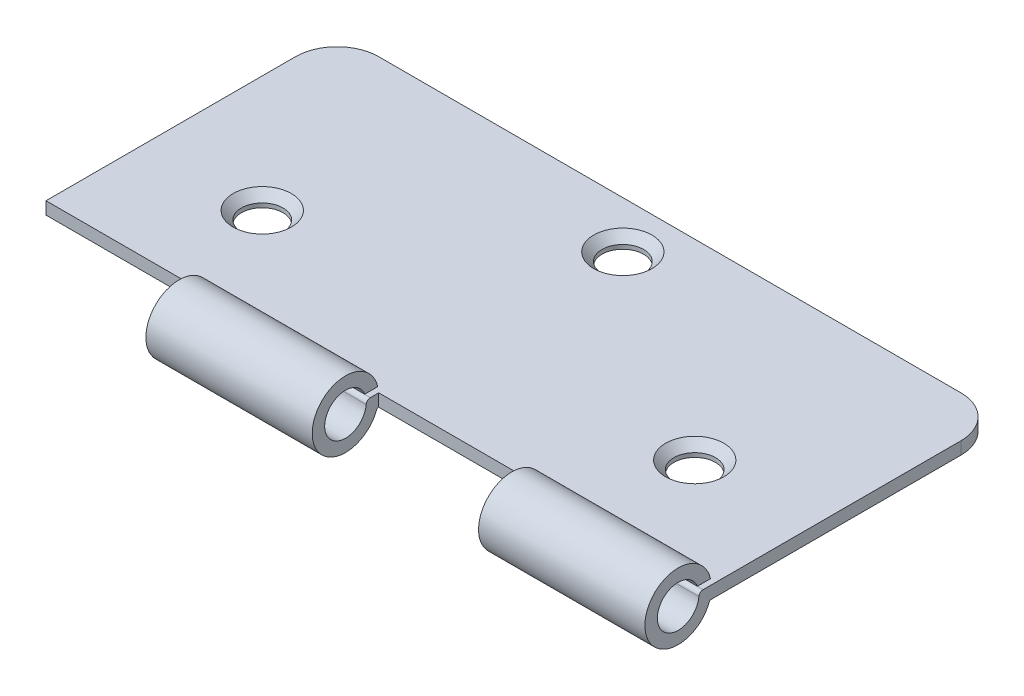
SolidWorks part; units mm, degrees
ref_plane "Front Plane" through (0, 0, 0) normal (0, 0, 1) x (1, 0, 0)
ref_plane "Top Plane" through (0, 0, 0) normal (0, 1, 0) x (1, 0, 0)
ref_plane "Right Plane" through (0, 0, 0) normal (1, 0, 0) x (0, 0, -1)
sketch "Sketch1" plane through (0, 0, 0) normal (0, 1, 0) x (1, 0, 0)
  line L1 (-40, -17.5) -> (40, -17.5)
  line L2 (-40, -17.5) -> (-40, 12.5)
  line L3 (-35, 17.5) -> (35, 17.5)
  line L4 (40, -17.5) -> (40, 12.5)
  line L5 (-40, -17.5) -> (40, 17.5) construction
  line L6 (-40, 17.5) -> (40, -17.5) construction
  arc A0 (35, 17.5) -> (40, 12.5) centre (35, 12.5) cw
  arc A1 (-40, 12.5) -> (-35, 17.5) centre (-35, 12.5) cw
  point P0 (0, 0)
  dimension "D3" = 5
  dimension "D1" = 80
  dimension "D2" = 35
extrude "Boss-Extrude1" add sketch "Sketch1" along normal blind 1.5
sketch "Sketch2" plane through (40, 0, 0) normal (1, 0, 0) x (0, 0, -1)
  line L0 (-17.5, 1.5) -> (-18.5043, 1.5)
  line L1 (-17.5, 0) -> (-17.5553, 0)
  line L2 (-19.1733, 2.1939) -> (-17.6031, 2.1939)
  line L3 (-17.5, 1.5) -> (-17.5, 0)
  arc A0 (-17.6031, 2.1939) -> (-17.7428, -0.1304) centre (-21.4929, 1.2614) ccw
  arc A1 (-19.1733, 2.1939) -> (-19.0024, 1.0436) centre (-21.4929, 1.2614) ccw
  arc A2 (-17.7428, -0.1304) -> (-17.5553, 0) centre (-17.5553, -0.2) cw
  arc A3 (-18.5043, 1.5) -> (-19.0024, 1.0436) centre (-18.5043, 1) ccw
  dimension "D1" = 8
  dimension "D2" = 5
  dimension "D3" = 0.2
  dimension "D4" = 0.5
extrude "Boss-Extrude2" add sketch "Sketch2" against normal blind 20
pattern_linear "LPattern1" count 2 spacing 40 along (-1, 0, 0) of "Boss-Extrude2"
sketch "Sketch3" plane through (0, 1.5, 0) normal (0, 1, 0) x (1, 0, 0)
  line L0 (-40, -17.5) -> (-20, -17.5) construction
  line L1 (0, -17.5) -> (20, -17.5) construction
  line L3 (40, -18.5043) -> (40, 12.5) construction
  line L4 (-40, 12.5) -> (-40, -17.5) construction
  circle A0 centre (-26, -5.5) radius 2.5
  circle A1 centre (26, -5.5) radius 2.5
  circle A2 centre (0, 11.8557) radius 2.5
  point P12 (40, -0.2102)
  dimension "D1" = 5
  dimension "D2" = 5
  dimension "D3" = 5
  dimension "D4" = 12
  dimension "D5" = 12
  dimension "D6" = 14
  dimension "D7" = 14
extrude "Cut-Extrude1" cut sketch "Sketch3" against normal through all
chamfer "Chamfer1" distance 1 angle 45 3 edges at (26, 1.5, 8) (0, 1.5, -9.3557) (-26, 1.5, 8)
